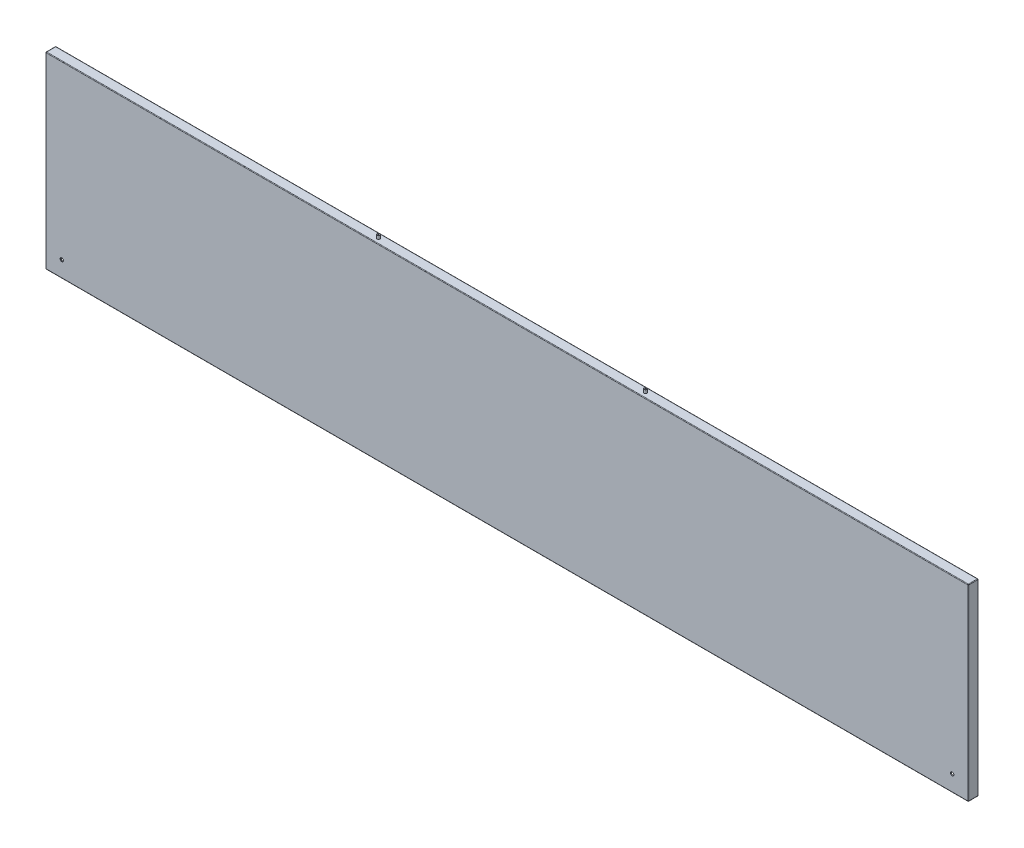
SolidWorks part; units mm, degrees
ref_plane "前视基准面" through (0, 0, 0) normal (0, 0, 1) x (1, 0, 0)
ref_plane "上视基准面" through (0, 0, 0) normal (0, 1, 0) x (1, 0, 0)
ref_plane "右视基准面" through (0, 0, 0) normal (1, 0, 0) x (0, 0, -1)
sketch "草图1" plane through (0, 0, 0) normal (0, 0, 1) x (1, 0, 0)
  line L1 (829, -169) -> (-829, -169)
  line L2 (829, -169) -> (829, 169)
  line L3 (829, 169) -> (-829, 169)
  line L4 (-829, -169) -> (-829, 169)
  line L5 (829, -169) -> (-829, 169) construction
  line L6 (829, 169) -> (-829, -169) construction
  point P0 (0, 0)
  dimension "D1" = 1658
  dimension "D2" = 338
extrude "凸台-拉伸1" add sketch "草图1" along normal blind 1.5
sketch "草图2" plane through (0, 0, 0) normal (0, 0, -1) x (-1, 0, 0)
  line L1 (-829, -169) -> (829, -169)
  line L2 (-829, -169) -> (-829, 169)
  line L3 (-829, 169) -> (829, 169)
  line L4 (829, -169) -> (829, 169)
  line L5 (-829, -169) -> (829, 169) construction
  line L6 (-829, 169) -> (829, -169) construction
  line L7 (-827.5, -167.5) -> (827.5, -167.5)
  line L8 (-827.5, -167.5) -> (-827.5, 167.5)
  line L9 (-827.5, 167.5) -> (827.5, 167.5)
  line L10 (827.5, -167.5) -> (827.5, 167.5)
  line L11 (-827.5, -167.5) -> (827.5, 167.5) construction
  line L12 (-827.5, 167.5) -> (827.5, -167.5) construction
  point P0 (0, 0)
  point P7 (0, 0)
  dimension "D1" = 1.5
  dimension "D2" = 1.5
extrude "凸台-拉伸2" add sketch "草图2" along normal blind 15
sketch "草图3" plane through (0, 0, -15) normal (0, 0, -1) x (-1, 0, 0)
  line L1 (-829, -169) -> (829, -169)
  line L2 (-829, -169) -> (-829, 169)
  line L3 (-829, 169) -> (829, 169)
  line L4 (829, -169) -> (829, 169)
  line L5 (-829, -169) -> (829, 169) construction
  line L6 (-829, 169) -> (829, -169) construction
  line L7 (-819, -159) -> (819, -159)
  line L8 (-819, -159) -> (-819, 159)
  line L9 (-819, 159) -> (819, 159)
  line L10 (819, -159) -> (819, 159)
  line L11 (-819, -159) -> (819, 159) construction
  line L12 (-819, 159) -> (819, -159) construction
  point P0 (0, 0)
  point P7 (0, 0)
  dimension "D1" = 10
  dimension "D2" = 10
extrude "凸台-拉伸3" add sketch "草图3" along normal blind 1.5
sketch "草图5" plane through (0, 169, 0) normal (0, 1, 0) x (1, 0, 0)
  line L0 (0, 0) -> (0, 19.0214) construction
  line L1 (829, -1.5) -> (-829, -1.5) construction
  circle A0 centre (240, 7.5) radius 1
  circle A1 centre (240, 7.5) radius 2.5
  circle A2 centre (-240, 7.5) radius 2.5
  circle A3 centre (-240, 7.5) radius 1
  dimension "D1" = 480
  dimension "D2" = 5
  dimension "D3" = 2
  dimension "D4" = 5
  dimension "D5" = 2
  dimension "D6" = 9
extrude "凸台-拉伸4" add sketch "草图5" along normal blind 6
sketch "草图6" plane through (0, 0, 1.5) normal (0, 0, 1) x (1, 0, 0)
  line L0 (0, -169) -> (0, 169) construction
  line L1 (-829, -169) -> (829, -169) construction
  line L2 (829, 169) -> (-829, 169) construction
  line L3 (829, -169) -> (829, 169) construction
  circle A0 centre (-800, -140) radius 3
  circle A1 centre (800, -140) radius 3
  dimension "D3" = 6
  dimension "D1" = 29
  dimension "D2" = 29
extrude "切除-拉伸1" cut sketch "草图6" against normal through all
fillet "圆角1" radius 1 12 edges at (0, -169, -16.5) (829, 0, -16.5) (0, 169, -16.5) (-829, 169, -7.5) (-829, 0, -16.5) (829, -169, -7.5) (-829, -169, -7.5) (-829, 0, 1.5) (0, -169, 1.5) (0, 169, 1.5) (829, 0, 1.5) (829, 169, -7.5)
